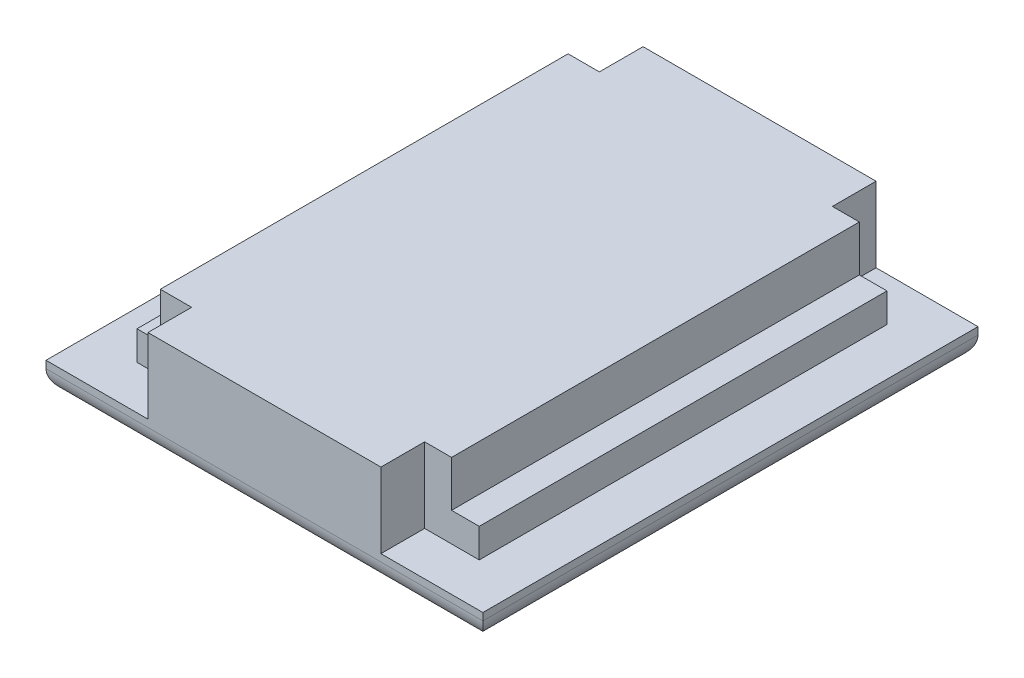
SolidWorks part; units mm, degrees
ref_plane "Front Plane" through (0, 0, 0) normal (0, 0, 1) x (1, 0, 0)
ref_plane "Top Plane" through (0, 0, 0) normal (0, 1, 0) x (1, 0, 0)
ref_plane "Right Plane" through (0, 0, 0) normal (1, 0, 0) x (0, 0, -1)
sketch "Sketch1" plane through (0, 0, 0) normal (0, 1, 0) x (1, 0, 0)
  line L1 (-19.2665, 11.2929) -> (18.8335, 11.2929)
  line L2 (-19.2665, 11.2929) -> (-19.2665, -31.8871)
  line L3 (-19.2665, -31.8871) -> (18.8335, -31.8871)
  line L4 (18.8335, 11.2929) -> (18.8335, -31.8871)
  dimension "D1" = 38.1
  dimension "D2" = 43.18
extrude "Boss-Extrude1" add sketch "Sketch1" along normal blind 2.54
sketch "Sketch2" plane through (0, 2.54, 0) normal (0, 1, 0) x (1, 0, 0)
  line L0 (18.8335, 11.2929) -> (-19.2665, 11.2929) construction
  line L1 (-15.139, 7.4829) -> (14.706, 7.4829)
  line L2 (-15.139, 7.4829) -> (-15.139, -28.0771)
  line L3 (-15.139, -28.0771) -> (14.706, -28.0771)
  line L4 (14.706, 7.4829) -> (14.706, -28.0771)
  line L5 (-19.2665, 11.2929) -> (-19.2665, -31.8871) construction
  dimension "D1" = 29.845
  dimension "D2" = 35.56
  dimension "D3" = 3.81
  dimension "D4" = 4.1275
extrude "Boss-Extrude2" add sketch "Sketch2" along normal blind 2.54
sketch "Sketch3" plane through (0, 5.08, 0) normal (0, 1, 0) x (1, 0, 0)
  line L0 (14.706, 7.4829) -> (-15.139, 7.4829) construction
  line L1 (-13.107, 7.4829) -> (12.293, 7.4829)
  line L2 (-13.107, 7.4829) -> (-13.107, -28.0771)
  line L3 (-13.107, -28.0771) -> (12.293, -28.0771)
  line L4 (12.293, 7.4829) -> (12.293, -28.0771)
  line L5 (-15.139, -28.0771) -> (14.706, -28.0771) construction
  line L6 (-15.139, 7.4829) -> (-15.139, -28.0771) construction
  dimension "D1" = 25.4
  dimension "D2" = 2.032
extrude "Boss-Extrude3" add sketch "Sketch3" along normal blind 4
sketch "Sketch7" plane through (0, 2.54, 0) normal (0, 1, 0) x (1, 0, 0)
  line L0 (-15.139, -28.0771) -> (14.706, -28.0771) construction
  line L1 (-10.3765, -28.0771) -> (9.9435, -28.0771)
  line L2 (-10.3765, -28.0771) -> (-10.3765, -31.8871)
  line L3 (-10.3765, -31.8871) -> (9.9435, -31.8871)
  line L4 (9.9435, -28.0771) -> (9.9435, -31.8871)
  line L5 (-19.2665, -31.8871) -> (18.8335, -31.8871) construction
  line L6 (18.8335, 11.2929) -> (-19.2665, 11.2929) construction
  line L7 (-10.3765, 11.2929) -> (9.9435, 11.2929)
  line L8 (-10.3765, 11.2929) -> (-10.3765, 7.4829)
  line L9 (-10.3765, 7.4829) -> (9.9435, 7.4829)
  line L10 (9.9435, 11.2929) -> (9.9435, 7.4829)
  line L11 (14.706, 7.4829) -> (-15.139, 7.4829) construction
  line L12 (-19.2665, 11.2929) -> (-19.2665, -31.8871) construction
  point P18 (-10.3765, -29.9821)
  point P19 (9.9435, -29.9821)
  dimension "D1" = 20.32
  dimension "D2" = 8.89
  dimension "D3" = 8.89
  dimension "D4" = 20.32
extrude "Boss-Extrude5" add sketch "Sketch7" along normal up to surface (6.54 mm away) up to face at (-0.407, 9.08, 10.2971)
fillet "Fillet1" radius 1.905 4 edges at (-0.2165, 0, 31.8871) (18.8335, 0, 10.2971) (-0.2165, 0, -11.2929) (-19.2665, 0, 10.2971)
